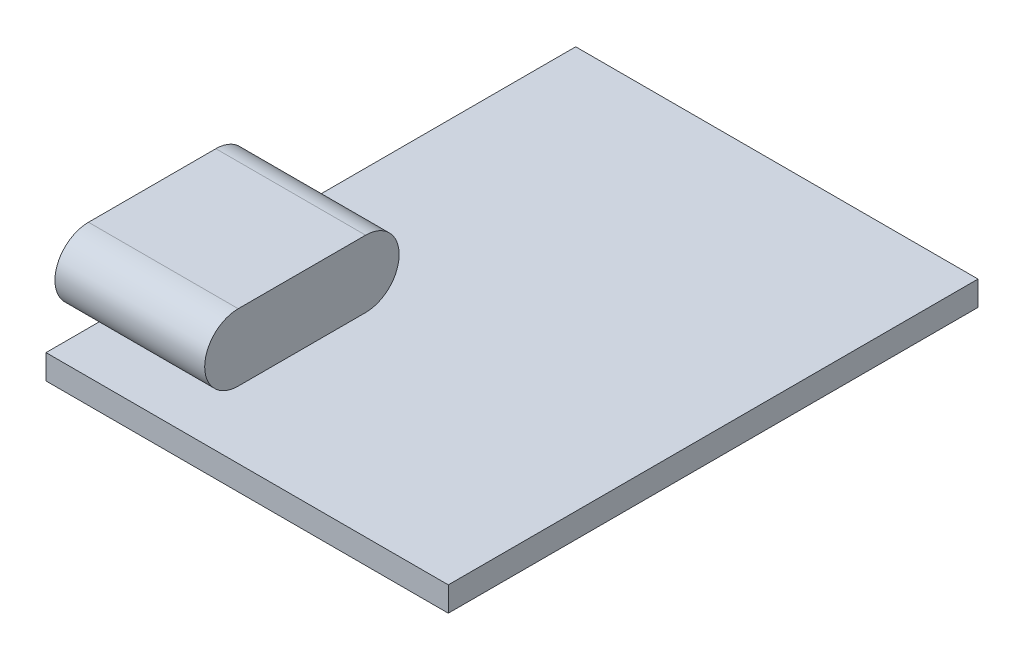
SolidWorks part; units mm, degrees
ref_plane "Plano frontal" through (0, 0, 0) normal (0, 0, 1) x (1, 0, 0)
ref_plane "Plano superior" through (0, 0, 0) normal (0, 1, 0) x (1, 0, 0)
ref_plane "Plano direito" through (0, 0, 0) normal (1, 0, 0) x (0, 0, -1)
sketch "Esboço1" plane through (0, 0, 0) normal (0, 1, 0) x (1, 0, 0)
  line L1 (0, 0) -> (18, 0)
  line L2 (0, 0) -> (0, 23.7)
  line L3 (0, 23.7) -> (18, 23.7)
  line L4 (18, 0) -> (18, 23.7)
  dimension "D1" = 23.7
  dimension "D2" = 18
extrude "Ressalto-extrusão1" add sketch "Esboço1" along normal blind 1.1
sketch "Esboço2" plane through (0, 0, 0) normal (-1, 0, 0) x (0, 0, 1)
  line L0 (-8.7, 2.6) -> (-3, 2.6) construction
  line L1 (-8.7, 4.1) -> (-3, 4.1)
  line L2 (-8.7, 1.1) -> (-3, 1.1)
  line L3 (-23.7, 1.1) -> (0, 1.1) construction
  line L5 (0, 1.1) -> (0, 0) construction
  arc A0 (-8.7, 4.1) -> (-8.7, 1.1) centre (-8.7, 2.6) ccw
  arc A1 (-3, 1.1) -> (-3, 4.1) centre (-3, 2.6) ccw
  point P2 (-5.85, 2.6)
  point P9 (-10.2, 2.6)
  point P10 (-1.5, 2.6)
  dimension "D1" = 3
  dimension "D2" = 8.7
  dimension "D3" = 1.5
extrude "Ressalto-extrusão2" add sketch "Esboço2" along normal blind 1.1 and the other way blind 5.6
